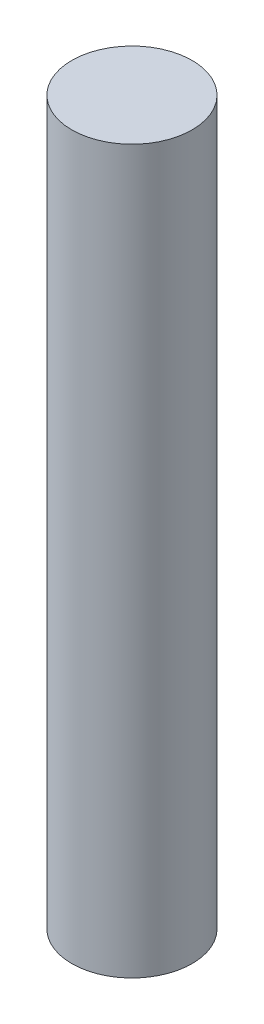
SolidWorks part; units mm, degrees
ref_plane "Front Plane" through (0, 0, 0) normal (0, 0, 1) x (1, 0, 0)
ref_plane "Top Plane" through (0, 0, 0) normal (0, 1, 0) x (1, 0, 0)
ref_plane "Right Plane" through (0, 0, 0) normal (1, 0, 0) x (0, 0, -1)
sketch "Sketch1" plane through (0, 0, 0) normal (0, 1, 0) x (1, 0, 0)
  circle A0 centre (0, 0) radius 2
  dimension "D1" = 4
extrude "Boss-Extrude1" add sketch "Sketch1" along normal blind 24 contours A0
